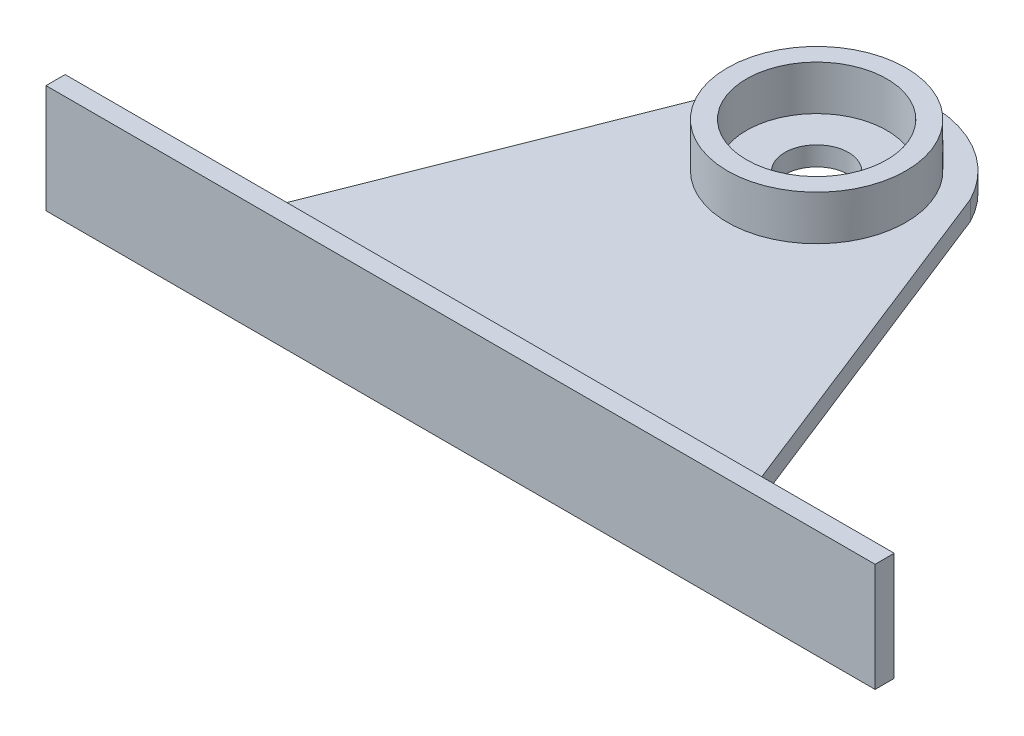
SolidWorks part; units mm, degrees
ref_plane "Front Plane" through (0, 0, 0) normal (0, 0, 1) x (1, 0, 0)
ref_plane "Top Plane" through (0, 0, 0) normal (0, 1, 0) x (1, 0, 0)
ref_plane "Right Plane" through (0, 0, 0) normal (1, 0, 0) x (0, 0, -1)
sketch "Sketch1" plane through (0, 0, 0) normal (0, 1, 0) x (1, 0, 0)
  line L0 (-48.9291, -17.8351) -> (31.0709, -17.8351)
  line L1 (31.0709, -17.8351) -> (6.9855, 43.197)
  line L2 (-24.8438, 43.197) -> (-48.9291, -17.8351)
  line L3 (-8.9291, -17.8351) -> (-8.9291, 35.0049) construction
  arc A0 (-24.8438, 43.197) -> (6.9855, 43.197) centre (-8.9291, 35.0049) cw
  circle A1 centre (-8.9291, 35.0049) radius 11 construction
  dimension "D3" = 22
  dimension "D1" = 80
  dimension "D4" = 52.84
extrude "Boss-Extrude1" add sketch "Sketch1" along normal blind 3
sketch "Sketch2" plane through (0, 3, 0) normal (0, 1, 0) x (1, 0, 0)
  circle A0 centre (-8.9291, 35.0049) radius 11
  circle A1 centre (-8.9291, 35.0049) radius 14
  dimension "D1" = 28
  dimension "D2" = 22
extrude "Boss-Extrude2" add sketch "Sketch2" along normal blind 7
sketch "Sketch3" plane through (0, 0, 17.8351) normal (0, 0, 1) x (1, 0, 0)
  line L1 (-73.9291, -7) -> (56.0709, -7)
  line L2 (-73.9291, -7) -> (-73.9291, 10)
  line L3 (-73.9291, 10) -> (56.0709, 10)
  line L4 (56.0709, -7) -> (56.0709, 10)
  line L6 (31.0709, 3) -> (31.0709, 0) construction
  dimension "D1" = 130
  dimension "D2" = 17
  dimension "D3" = 25
extrude "Boss-Extrude3" add sketch "Sketch3" along normal blind 3
sketch "Sketch4" plane through (0, 0, 17.8351) normal (0, 0, -1) x (-1, 0, 0)
  line L0 (-56.0709, 10) -> (73.9291, 10) construction
  circle A0 centre (-23.299, 6.5) radius 2.5726
  dimension "D2" = 5.1453
  dimension "D1" = 3.5
sketch "Sketch5" plane through (0, 3, 0) normal (0, 1, 0) x (1, 0, 0)
  circle A0 centre (-8.9291, 35.0049) radius 5
  dimension "D1" = 10
extrude "Cut-Extrude1" cut sketch "Sketch5" against normal blind 10
